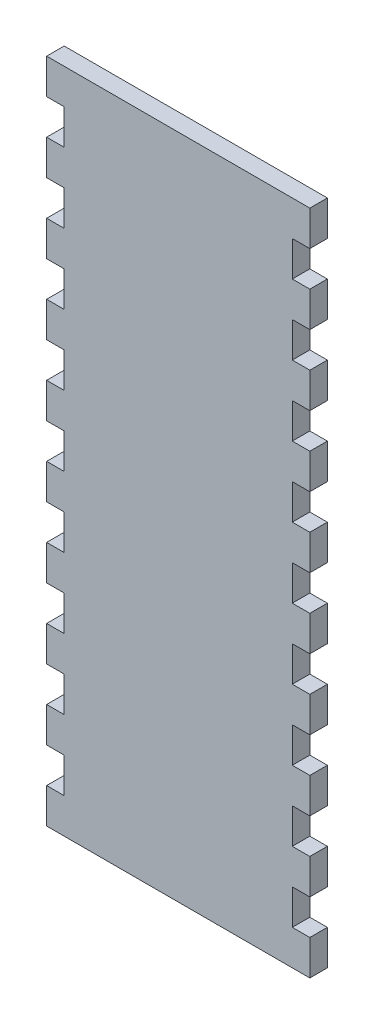
SolidWorks part; units mm, degrees
material "Pine"
ref_plane "Front Plane" through (0, 0, 0) normal (0, 0, 1) x (1, 0, 0)
ref_plane "Top Plane" through (0, 0, 0) normal (0, 1, 0) x (1, 0, 0)
ref_plane "Right Plane" through (0, 0, 0) normal (1, 0, 0) x (0, 0, -1)
sketch "Sketch1" plane through (0, 0, 0) normal (0, 0, 1) x (1, 0, 0)
  line L1 (0, 0) -> (95.25, 0)
  line L2 (0, 0) -> (0, 241.3)
  line L3 (0, 241.3) -> (95.25, 241.3)
  line L4 (95.25, 0) -> (95.25, 241.3)
  dimension "D1" = 95.25
  dimension "D2" = 241.3
extrude "Boss-Extrude1" add sketch "Sketch1" along normal blind 6.35 contours L2 L3 L4 L1
sketch "Sketch2" plane through (0, 0, 6.35) normal (0, 0, 1) x (1, 0, 0)
  line L0 (0, 0) -> (0, 241.3) construction
  line L1 (0, 228.6) -> (6.35, 228.6)
  line L2 (0, 228.6) -> (0, 215.9)
  line L3 (0, 215.9) -> (6.35, 215.9)
  line L4 (6.35, 228.6) -> (6.35, 215.9)
  line L5 (95.25, 0) -> (95.25, 241.3) construction
  line L6 (95.25, 228.6) -> (88.9, 228.6)
  line L7 (95.25, 228.6) -> (95.25, 215.9)
  line L8 (95.25, 215.9) -> (88.9, 215.9)
  line L9 (88.9, 228.6) -> (88.9, 215.9)
  line L10 (0, 241.3) -> (95.25, 241.3) construction
  dimension "D1" = 12.7
  dimension "D2" = 12.7
  dimension "D3" = 6.35
extrude "Cut-Extrude1" cut sketch "Sketch2" against normal through all
pattern_linear "LPattern1" count 9 spacing 25.4 along (0, -1, 0) of "Cut-Extrude1"
